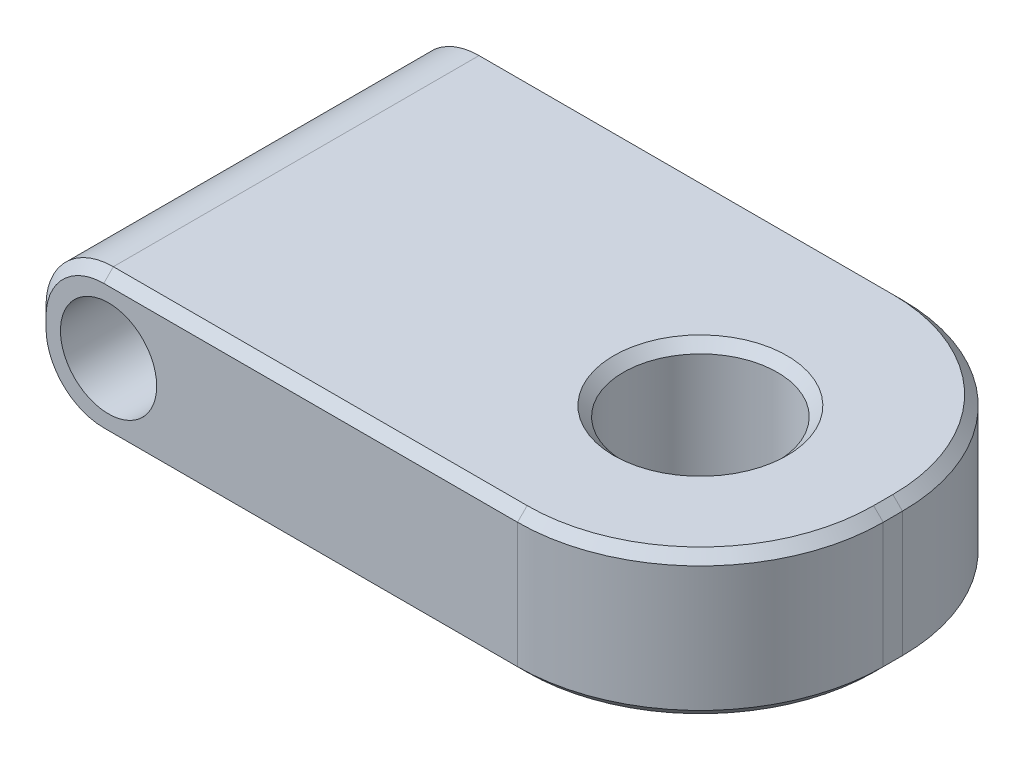
SolidWorks part; units mm, degrees
material "6061 Alloy"
ref_plane "Front Plane" through (0, 0, 0) normal (0, 0, 1) x (1, 0, 0)
ref_plane "Top Plane" through (0, 0, 0) normal (0, 1, 0) x (1, 0, 0)
ref_plane "Right Plane" through (0, 0, 0) normal (1, 0, 0) x (0, 0, -1)
sketch "Sketch1" plane through (0, 0, 0) normal (0, 1, 0) x (1, 0, 0)
  line L1 (15.5, -20) -> (-34.5, -20)
  line L2 (34.5, -1) -> (34.5, 1)
  line L3 (15.5, 20) -> (-34.5, 20)
  line L4 (-34.5, -20) -> (-34.5, 20)
  line L5 (34.5, -20) -> (-34.5, 20) construction
  line L6 (34.5, 20) -> (-34.5, -20) construction
  arc A0 (15.5, -20) -> (34.5, -1) centre (15.5, -1) ccw
  arc A1 (34.5, 1) -> (15.5, 20) centre (15.5, 1) ccw
  point P0 (0, 0)
  dimension "D2" = 19
  dimension "D1" = 40
  dimension "D3" = 50
extrude "Boss-Extrude1" add sketch "Sketch1" along normal blind 15
sketch "Sketch2" plane through (0, 0, 20) normal (0, 0, 1) x (1, 0, 0)
  line L0 (-34.5, 15) -> (-34.5, 0) construction
  circle A0 centre (-27, 7.5) radius 5
  dimension "D1" = 10
  dimension "D2" = 7.5
extrude "Cut-Extrude1" cut sketch "Sketch2" against normal through all
fillet "Fillet1" radius 7 2 edges at (-34.5, 0, 0) (-34.5, 15, 0)
sketch "Sketch3" plane through (0, 15, 0) normal (0, 1, 0) x (1, 0, 0)
  circle A0 centre (15.5, -1) radius 8
  dimension "D1" = 16
extrude "Cut-Extrude2" cut sketch "Sketch3" against normal through all
chamfer "Chamfer1" distance 1 angle 45 18 edges at (28.935, 0, 14.435) (28.935, 0, -14.435) (34.5, 0, 0) (-6, 0, -20) (-32.4497, 2.0503, -20) (-6, 0, 20) (-34.5, 7.5, -20) (-32.4497, 2.0503, 20) (-32.4497, 12.9497, -20) (-34.5, 7.5, 20) (-6, 15, -20) (-32.4497, 12.9497, 20) (28.935, 15, -14.435) (-6, 15, 20) (34.5, 15, 0) (28.935, 15, 14.435) (15.5, 0, 9) (15.5, 15, 9)
